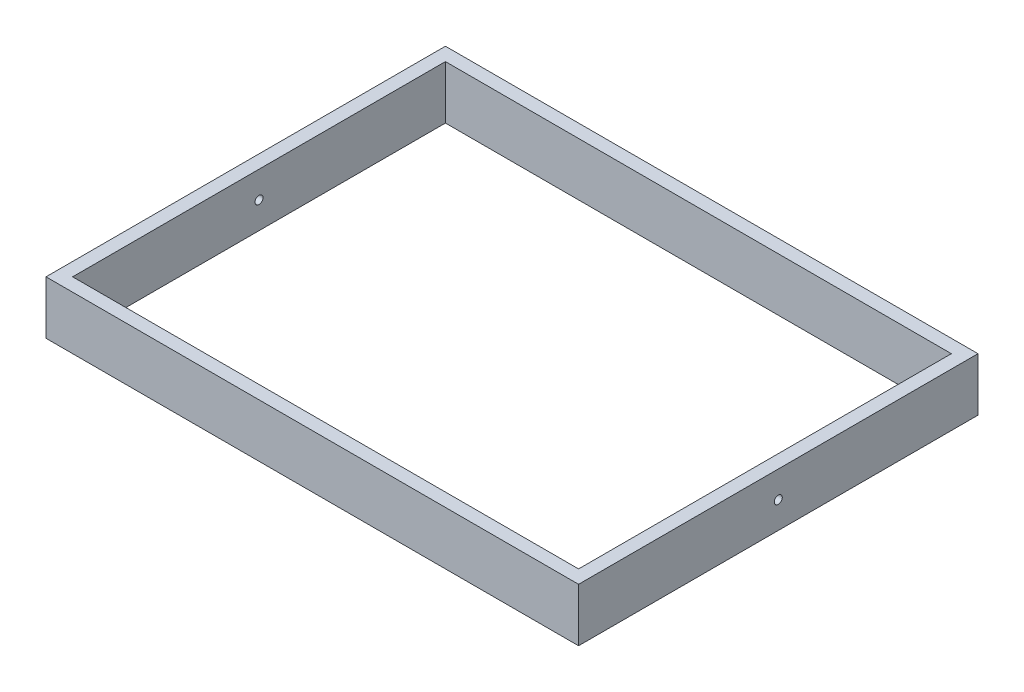
SolidWorks part; units mm, degrees
ref_plane "Front Plane" through (0, 0, 0) normal (0, 0, 1) x (1, 0, 0)
ref_plane "Top Plane" through (0, 0, 0) normal (0, 1, 0) x (1, 0, 0)
ref_plane "Right Plane" through (0, 0, 0) normal (1, 0, 0) x (0, 0, -1)
sketch "Sketch1" plane through (0, 0, 0) normal (0, 1, 0) x (1, 0, 0)
  line L0 (-190, 140) -> (190, 140)
  line L1 (-200, -150) -> (200, -150)
  line L2 (-200, -150) -> (-200, 150)
  line L3 (-200, 150) -> (200, 150)
  line L4 (200, -150) -> (200, 150)
  line L5 (-200, -150) -> (200, 150) construction
  line L6 (-200, 150) -> (200, -150) construction
  line L7 (190, -140) -> (190, 140)
  line L8 (-190, -140) -> (190, -140)
  line L9 (-190, -140) -> (-190, 140)
  point P1 (0, 0)
  dimension "D1" = 400
  dimension "D2" = 300
  dimension "D3" = 10
extrude "Boss-Extrude1" add sketch "Sketch1" along normal blind 40
sketch "Sketch2" plane through (200, 0, 0) normal (1, 0, 0) x (0, 0, -1)
  line L0 (-150, 0) -> (150, 0) construction
  line L1 (150, 40) -> (150, 0) construction
  circle A0 centre (0, 20) radius 3
  dimension "D1" = 20
  dimension "D3" = 6
  dimension "D2" = 150
sketch "Sketch4" plane through (-200, 0, 0) normal (-1, 0, 0) x (0, 0, 1)
  line L0 (-150, 0) -> (150, 0) construction
  line L1 (150, 40) -> (150, 0) construction
  circle A0 centre (110, 20) radius 3
  point P4 (150, 20)
  dimension "D3" = 6
  dimension "D1" = 20
  dimension "D2" = 40
extrude "Boss-Extrude4" add sketch "Sketch4" along normal blind 10
extrude "Cut-Extrude1" cut sketch "Sketch2" against normal up to surface (400 mm away) up to face at (-200, 20, 0)
